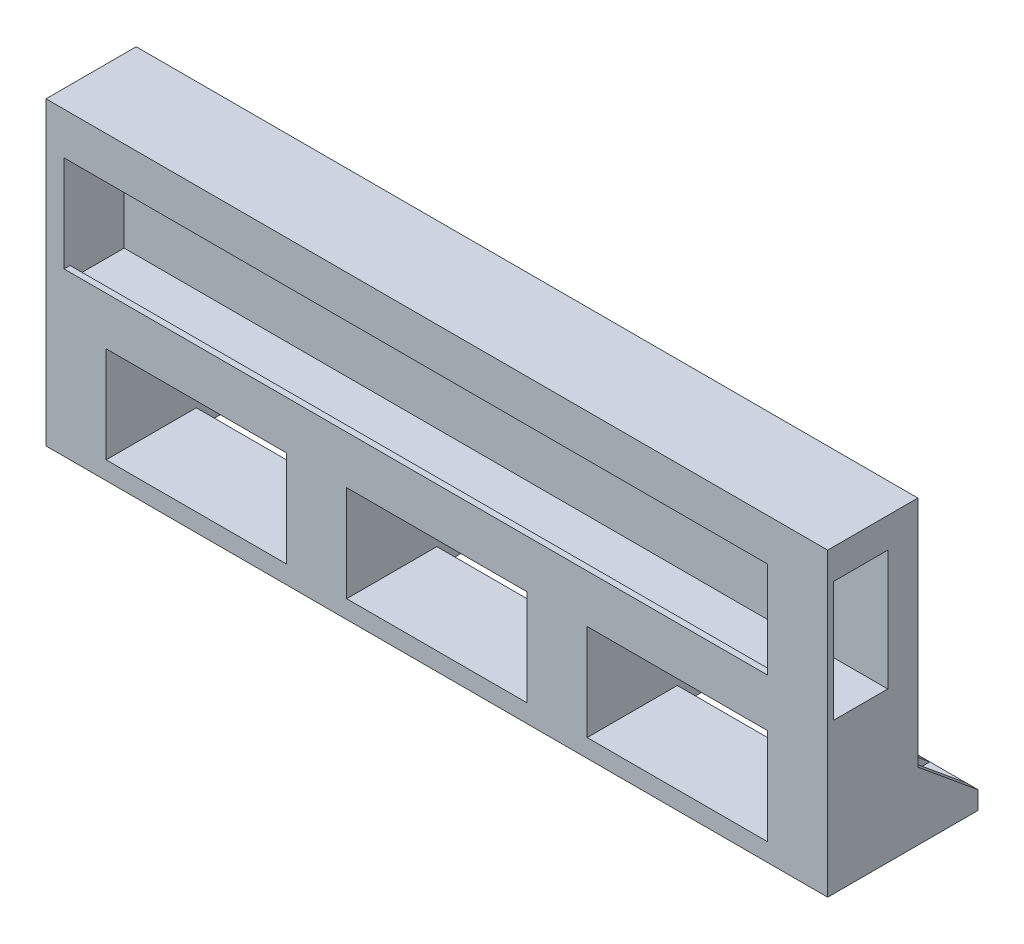
SolidWorks part; units mm, degrees
ref_plane "Front Plane" through (0, 0, 0) normal (0, 0, 1) x (1, 0, 0)
ref_plane "Top Plane" through (0, 0, 0) normal (0, 1, 0) x (1, 0, 0)
ref_plane "Right Plane" through (0, 0, 0) normal (1, 0, 0) x (0, 0, -1)
sketch "Sketch1" plane through (0, 0, 0) normal (0, 0, 1) x (1, 0, 0)
  line L1 (-215.8491, 80) -> (-85.8491, 80)
  line L2 (-215.8491, 80) -> (-215.8491, 130)
  line L3 (-215.8491, 130) -> (-85.8491, 130)
  line L4 (-85.8491, 80) -> (-85.8491, 130)
  dimension "D1" = 50
  dimension "D2" = 130
extrude "Boss-Extrude1" add sketch "Sketch1" along normal blind 15
sketch "Sketch3" plane through (-85.8491, 0, 0) normal (1, 0, 0) x (0, 0, -1)
  line L1 (-14, 125) -> (-5, 125)
  line L2 (-14, 125) -> (-14, 123)
  line L3 (-14, 105) -> (-5, 105)
  line L4 (-5, 125) -> (-5, 105)
  line L5 (-15, 80) -> (0, 80) construction
  line L6 (0, 80) -> (0, 130) construction
  line L7 (-14, 123) -> (-15, 123)
  line L8 (-15, 80) -> (-15, 130) construction
  line L9 (-15, 123) -> (-15, 107)
  line L10 (-15, 107) -> (-14, 107)
  line L11 (-14, 107) -> (-14, 105)
  dimension "D1" = 20
  dimension "D2" = 9
  dimension "D3" = 25
  dimension "D4" = 5
  dimension "D5" = 1
  dimension "D6" = 2
  dimension "D7" = 2
extrude "Cut-Extrude1" cut sketch "Sketch3" against normal blind 127 and the other way through all
sketch "Sketch4" plane through (0, 0, 0) normal (0, 0, -1) x (-1, 0, 0)
  line L0 (215.8491, 80) -> (85.8491, 80) construction
  line L1 (100.8491, 80) -> (110.8491, 80)
  line L2 (100.8491, 80) -> (100.8491, 83)
  line L3 (100.8491, 83) -> (110.8491, 83)
  line L4 (110.8491, 80) -> (110.8491, 83)
  line L5 (85.8491, 80) -> (85.8491, 130) construction
  line L6 (190.8491, 80) -> (200.8491, 80)
  line L7 (190.8491, 80) -> (190.8491, 83)
  line L8 (190.8491, 83) -> (200.8491, 83)
  line L9 (200.8491, 80) -> (200.8491, 83)
  line L10 (215.8491, 130) -> (215.8491, 80) construction
  dimension "D1" = 3
  dimension "D2" = 10
  dimension "D3" = 10
  dimension "D4" = 3
  dimension "D5" = 15
  dimension "D6" = 15
extrude "Boss-Extrude2" add sketch "Sketch4" along normal blind 10
sketch "Sketch6" plane through (0, 0, 0) normal (0, 0, -1) x (-1, 0, 0)
  line L5 (215.8491, 130) -> (215.8491, 80) construction
  line L6 (205.8491, 83) -> (175.8491, 83)
  line L7 (205.8491, 83) -> (205.8491, 99)
  line L8 (205.8491, 99) -> (175.8491, 99)
  line L9 (175.8491, 83) -> (175.8491, 99)
  line L10 (165.8491, 83) -> (135.8491, 83)
  line L11 (165.8491, 83) -> (165.8491, 99)
  line L12 (165.8491, 99) -> (135.8491, 99)
  line L13 (135.8491, 83) -> (135.8491, 99)
  line L14 (125.8491, 99) -> (95.8491, 99)
  line L15 (125.8491, 99) -> (125.8491, 83)
  line L16 (125.8491, 83) -> (95.8491, 83)
  line L17 (95.8491, 99) -> (95.8491, 83)
  line L18 (85.8491, 80) -> (85.8491, 107) construction
  line L19 (215.8491, 80) -> (85.8491, 80) construction
  line L20 (212.8491, 107) -> (85.8491, 107) construction
  dimension "D1" = 10
  dimension "D2" = 10
  dimension "D3" = 10
  dimension "D4" = 30
  dimension "D5" = 30
  dimension "D6" = 10
  dimension "D7" = 30
  dimension "D8" = 3
  dimension "D9" = 8
extrude "Cut-Extrude2" cut sketch "Sketch6" against normal through all
sketch "Sketch7" plane through (0, 83, 0) normal (0, 1, 0) x (1, 0, 0)
  line L0 (-110.8491, 10) -> (-110.8491, 0) construction
  line L1 (-110.8491, 10) -> (-100.8491, 10) construction
  circle A0 centre (-105.8491, 5) radius 1.375
  dimension "D1" = 2.75
  dimension "D2" = 5
  dimension "D3" = 5
extrude "Cut-Extrude3" cut sketch "Sketch7" against normal through all
ref_plane "Plane1" through (-151, 0, 0) normal (1, 0, 0) x (0, 0, -1)
mirror "Mirror1" about plane through (-151, 0, 0) normal (1, 0, 0) of "Cut-Extrude3"
sketch "Sketch9" plane through (0, 0, 0) normal (0, 0, -1) x (-1, 0, 0)
  line L0 (190.8491, 80) -> (110.8491, 80) construction
  line L1 (145.8491, 80) -> (155.8491, 80)
  line L2 (145.8491, 80) -> (145.8491, 83)
  line L3 (145.8491, 83) -> (155.8491, 83)
  line L4 (155.8491, 80) -> (155.8491, 83)
  line L5 (135.8491, 83) -> (165.8491, 83) construction
  line L7 (150.8491, 83) -> (150.8491, 101.1506) construction
  dimension "D1" = 3
  dimension "D2" = 10
extrude "Boss-Extrude4" add sketch "Sketch9" along normal blind 10
sketch "Sketch10" plane through (0, 83, 0) normal (0, 1, 0) x (1, 0, 0)
  line L0 (-155.8491, 10) -> (-155.8491, 0) construction
  line L1 (-155.8491, 10) -> (-145.8491, 10) construction
  circle A0 centre (-150.8491, 5) radius 1.375
  dimension "D1" = 2.75
  dimension "D2" = 5
  dimension "D3" = 5
extrude "Cut-Extrude4" cut sketch "Sketch10" against normal blind 10
sketch "Sketch11" plane through (0, 107, 0) normal (0, 1, 0) x (1, 0, 0)
  line L0 (-85.8491, -14) -> (-212.8491, -14) construction
  line L1 (-85.8491, -15) -> (-95.8491, -15)
  line L2 (-85.8491, -15) -> (-85.8491, -14)
  line L3 (-85.8491, -14) -> (-95.8491, -14)
  line L4 (-95.8491, -15) -> (-95.8491, -14)
  dimension "D1" = 10
extrude "Boss-Extrude5" add sketch "Sketch11" along normal blind 20
sketch "Sketch13" plane through (0, 0, -10) normal (0, 0, -1) x (-1, 0, 0)
  line L0 (100.8491, 83) -> (110.8491, 83)
  line L1 (110.8491, 83) -> (110.8491, 80)
  line L2 (110.8491, 80) -> (100.8491, 80)
  line L3 (100.8491, 80) -> (100.8491, 83)
extrude "Cut-Extrude5" cut sketch "Sketch13" against normal blind 10
sketch "Sketch14" plane through (0, 0, -10) normal (0, 0, -1) x (-1, 0, 0)
  line L0 (145.8491, 83) -> (155.8491, 83)
  line L1 (155.8491, 83) -> (155.8491, 80)
  line L2 (155.8491, 80) -> (145.8491, 80)
  line L3 (145.8491, 80) -> (145.8491, 83)
extrude "Cut-Extrude6" cut sketch "Sketch14" against normal blind 10
sketch "Sketch15" plane through (0, 0, -10) normal (0, 0, -1) x (-1, 0, 0)
  line L0 (190.8491, 83) -> (200.8491, 83)
  line L1 (200.8491, 83) -> (200.8491, 80)
  line L2 (200.8491, 80) -> (190.8491, 80)
  line L3 (190.8491, 80) -> (190.8491, 83)
extrude "Cut-Extrude7" cut sketch "Sketch15" against normal blind 10
sketch "Sketch16" plane through (0, 0, 0) normal (0, 0, -1) x (-1, 0, 0)
  line L0 (85.8491, 80) -> (95.8491, 80)
  line L1 (215.8491, 80) -> (85.8491, 80) construction
  line L2 (95.8491, 80) -> (95.8491, 83)
  line L3 (95.8491, 83) -> (85.8491, 83)
  line L4 (85.8491, 80) -> (85.8491, 130) construction
  line L5 (85.8491, 83) -> (85.8491, 80)
  line L6 (135.8491, 99) -> (135.8491, 83) construction
  line L7 (125.8491, 83) -> (135.8491, 83)
  line L8 (125.8491, 83) -> (125.8491, 80)
  line L9 (125.8491, 80) -> (135.8491, 80)
  line L10 (135.8491, 83) -> (135.8491, 80)
  line L11 (175.8491, 99) -> (175.8491, 83) construction
  line L12 (165.8491, 83) -> (175.8491, 83)
  line L13 (165.8491, 83) -> (165.8491, 80)
  line L14 (165.8491, 80) -> (175.8491, 80)
  line L15 (175.8491, 83) -> (175.8491, 80)
  line L16 (205.8491, 83) -> (215.8491, 83)
  line L17 (205.8491, 83) -> (205.8491, 80)
  line L18 (205.8491, 80) -> (215.8491, 80)
  line L19 (215.8491, 83) -> (215.8491, 80)
extrude "Boss-Extrude6" add sketch "Sketch16" along normal blind 10
sketch "Sketch18" plane through (-85.8491, 0, 0) normal (1, 0, 0) x (0, 0, -1)
  line L0 (10, 83) -> (0, 91.2363)
  line L1 (0, 83) -> (0, 130) construction
  line L2 (0, 91.2363) -> (0, 83)
  line L3 (0, 83) -> (10, 83)
extrude "Boss-Extrude8" add sketch "Sketch18" against normal blind 10
ref_plane "Plane2" through (-125.8491, 83, 0) normal (0, 0, 1) x (1, 0, 0)
sketch "Sketch20" plane through (-125.8491, 0, 0) normal (1, 0, 0) x (0, 0, -1)
  line L0 (0, 83) -> (0, 91)
  line L1 (0, 83) -> (0, 99) construction
  line L2 (0, 91) -> (10, 83)
  line L3 (10, 83) -> (0, 83)
extrude "Boss-Extrude9" add sketch "Sketch20" against normal blind 10
sketch "Sketch21" plane through (-165.8491, 0, 0) normal (1, 0, 0) x (0, 0, -1)
  line L0 (0, 83) -> (0, 91)
  line L1 (0, 83) -> (0, 99) construction
  line L2 (0, 91) -> (10, 83)
  line L3 (10, 83) -> (0, 83)
extrude "Boss-Extrude10" add sketch "Sketch21" against normal blind 10
sketch "Sketch22" plane through (-205.8491, 0, 0) normal (1, 0, 0) x (0, 0, -1)
  line L0 (0, 83) -> (0, 91)
  line L1 (0, 83) -> (0, 99) construction
  line L2 (0, 91) -> (10, 83)
  line L3 (10, 83) -> (0, 83)
extrude "Boss-Extrude11" add sketch "Sketch22" against normal blind 10
sketch "Sketch29" plane through (0, 0, -10) normal (0, 0, -1) x (-1, 0, 0)
  line L0 (93.8491, 83) -> (93.8491, 93)
  line L1 (95.8491, 83) -> (85.8491, 83) construction
  line L2 (87.8491, 83) -> (93.8491, 83)
  line L3 (93.8491, 93) -> (87.8491, 93)
  line L4 (87.8491, 93) -> (87.8491, 83)
extrude "Cut-Extrude10" cut sketch "Sketch29" against normal blind 10
sketch "Sketch30" plane through (0, 0, -10) normal (0, 0, -1) x (-1, 0, 0)
  line L0 (133.8491, 83) -> (133.8491, 93)
  line L1 (135.8491, 83) -> (125.8491, 83) construction
  line L2 (127.8491, 83) -> (133.8491, 83)
  line L3 (133.8491, 93) -> (127.8491, 93)
  line L4 (127.8491, 93) -> (127.8491, 83)
extrude "Cut-Extrude11" cut sketch "Sketch30" against normal blind 10
sketch "Sketch31" plane through (0, 0, -10) normal (0, 0, -1) x (-1, 0, 0)
  line L0 (173.8491, 83) -> (173.8491, 93)
  line L1 (175.8491, 83) -> (165.8491, 83) construction
  line L2 (167.8491, 83) -> (173.8491, 83)
  line L3 (173.8491, 93) -> (167.8491, 93)
  line L4 (167.8491, 93) -> (167.8491, 83)
extrude "Cut-Extrude12" cut sketch "Sketch31" against normal blind 10
sketch "Sketch32" plane through (0, 0, -10) normal (0, 0, -1) x (-1, 0, 0)
  line L1 (215.8491, 83) -> (205.8491, 83) construction
  line L2 (207.8491, 83) -> (213.8491, 83)
  line L3 (207.8491, 83) -> (207.8491, 93)
  line L4 (207.8491, 93) -> (213.8491, 93)
  line L5 (213.8491, 93) -> (213.8491, 83)
extrude "Cut-Extrude13" cut sketch "Sketch32" against normal blind 10
sketch "Sketch33" plane through (0, 83, 0) normal (0, 1, 0) x (1, 0, 0)
  line L0 (-207.8491, 10) -> (-210.8491, 10)
  line L1 (-207.8491, 10) -> (-213.8491, 10) construction
  line L2 (-210.8491, 10) -> (-210.8491, 5)
  point P5 (0, 0)
  point P7 (0, 0)
sketch "Sketch35" plane through (0, 83, 0) normal (0, 1, 0) x (1, 0, 0)
  circle A0 centre (-210.8491, 5) radius 1.4
  circle A1 centre (-170.8491, 5) radius 1.4
  circle A2 centre (-130.8491, 5) radius 1.4
  circle A3 centre (-90.8491, 5) radius 1.4
  dimension "D1" = 2
  dimension "D2" = 2
extrude "Cut-Extrude14" cut sketch "Sketch35" against normal blind 5
